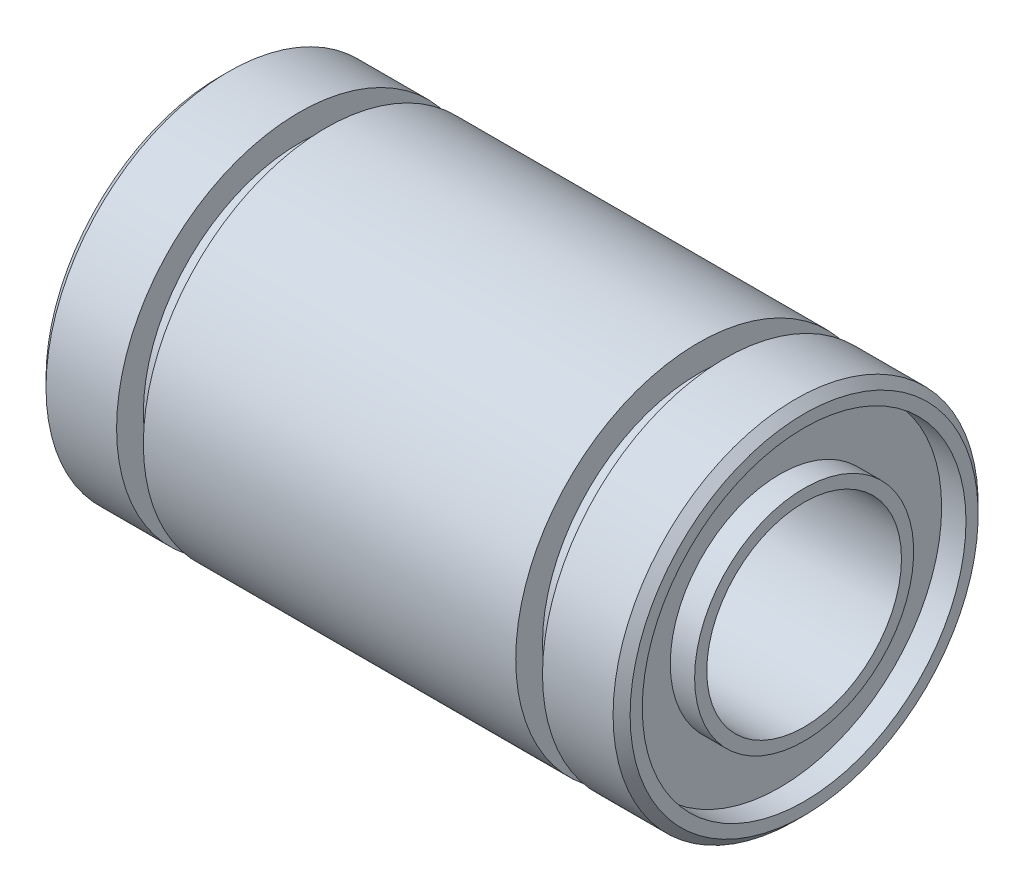
SolidWorks part; units mm, degrees
material "1060 Alloy"
ref_plane "Front Plane" through (0, 0, 0) normal (0, 0, 1) x (1, 0, 0)
ref_plane "Top Plane" through (0, 0, 0) normal (0, 1, 0) x (1, 0, 0)
ref_plane "Right Plane" through (0, 0, 0) normal (1, 0, 0) x (0, 0, -1)
sketch "Sketch1" plane through (0, 0, 0) normal (0, 0, 1) x (1, 0, 0)
  line L0 (-45.6895, 0) -> (45.6895, 0) construction
  line L1 (-11.65, 7.5) -> (-8.75, 7.5)
  line L2 (-8.75, 7.5) -> (-8.75, 6.4)
  line L3 (-8.75, 6.4) -> (-7.65, 6.4)
  line L4 (-7.65, 6.4) -> (-7.65, 7.5)
  line L5 (-7.65, 7.5) -> (7.65, 7.5)
  line L6 (0, 45.6895) -> (0, -45.6895) construction
  line L7 (-11.65, 7.5) -> (-12, 7.15)
  line L8 (-12, 7.15) -> (-12, 6.65)
  line L9 (-12, 6.65) -> (-11, 6.65)
  line L10 (-11, 6.65) -> (-11, 4.5)
  line L11 (-11, 4.5) -> (-12, 4.5)
  line L12 (-12, 4.5) -> (-12, 4)
  line L13 (-12, 4) -> (12, 4)
  line L14 (12, 4.5) -> (12, 4)
  line L15 (11, 4.5) -> (12, 4.5)
  line L16 (11, 6.65) -> (11, 4.5)
  line L17 (12, 6.65) -> (11, 6.65)
  line L18 (12, 7.15) -> (12, 6.65)
  line L19 (11.65, 7.5) -> (12, 7.15)
  line L20 (7.65, 6.4) -> (7.65, 7.5)
  line L21 (8.75, 6.4) -> (7.65, 6.4)
  line L22 (8.75, 7.5) -> (8.75, 6.4)
  line L23 (11.65, 7.5) -> (8.75, 7.5)
  point P19 (0, 4)
  point P26 (0, 7.5)
  dimension "D1" = 45
  dimension "D2" = 1.1
  dimension "D3" = 0.5
  dimension "L" = 24
  dimension "B" = 17.5
  dimension "W" = 1.1
  dimension "D" = 7.5
  dimension "D_1" = 7.15
  dimension "D4" = 0.5
  dimension "dr" = 4
  dimension "D5" = 1
revolve "Revolve1" add sketch "Sketch1" angle 360 about L0
equation "\"D\"=15"
equation "\"D1\"=14.3"
equation "\"dr\"=8"
equation "\"L\"=24"
equation "\"B\"=17.5"
equation "\"W\"=1.1"
equation "\"L@Sketch1\"= \"L\""
equation "\"B@Sketch1\"= \"B\""
equation "\"W@Sketch1\"= \"W\""
equation "\"dr@Sketch1\"= \"dr\" * 0.5"
equation "\"D@Sketch1\" = \"D\" * 0.5"
equation "\"D_1@Sketch1\" = \"D1\" * 0.5"
